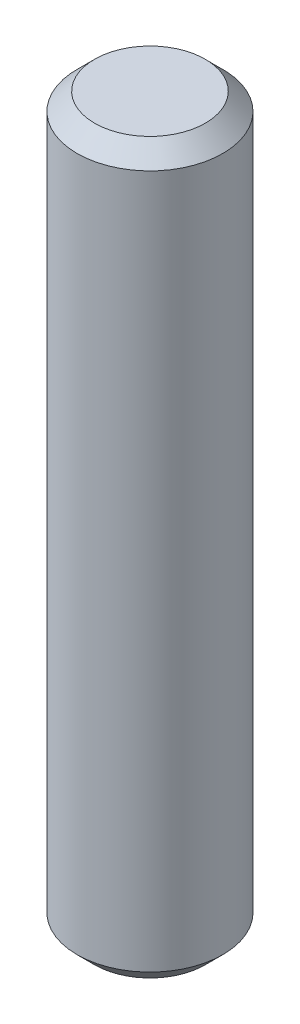
SolidWorks part; units mm, degrees
ref_plane "Front Plane" through (0, 0, 0) normal (0, 0, 1) x (1, 0, 0)
ref_plane "Top Plane" through (0, 0, 0) normal (0, 1, 0) x (1, 0, 0)
ref_plane "Right Plane" through (0, 0, 0) normal (1, 0, 0) x (0, 0, -1)
sketch "Sketch1" plane through (0, 0, 0) normal (0, 1, 0) x (1, 0, 0)
  circle A0 centre (0, 0) radius 6.35
  dimension "D1" = 12.7
extrude "Boss-Extrude1" add sketch "Sketch1" along normal blind 63.5
chamfer "Chamfer1" distance 1.524 angle 45 2 edges at (0, 0, 6.35) (0, 63.5, 6.35)
